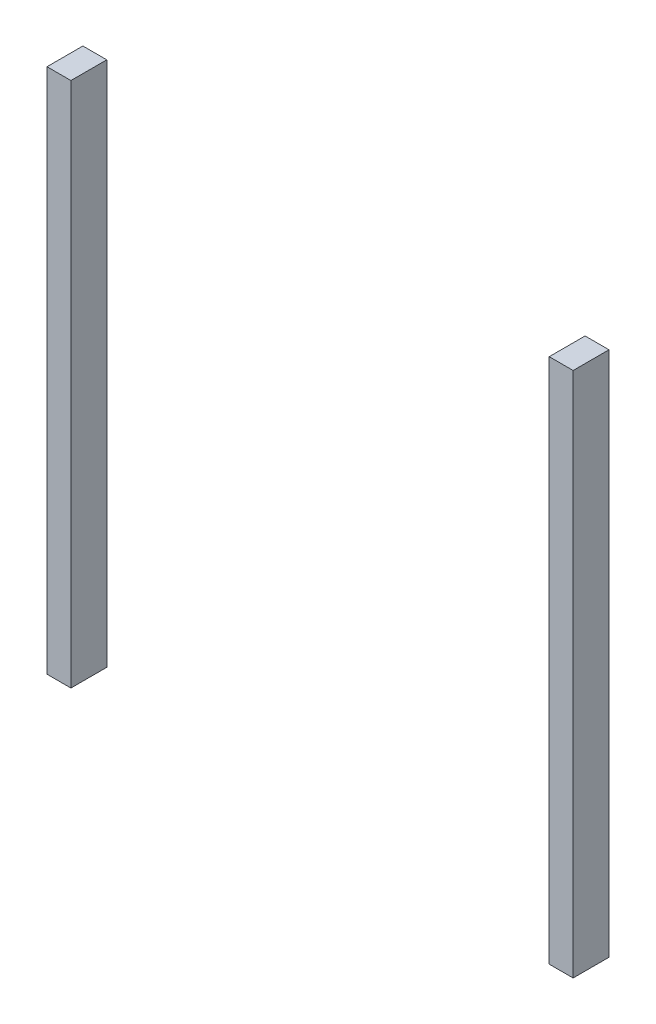
SolidWorks part; units mm, degrees
ref_plane "Front Plane" through (0, 0, 0) normal (0, 0, 1) x (1, 0, 0)
ref_plane "Top Plane" through (0, 0, 0) normal (0, 1, 0) x (1, 0, 0)
ref_plane "Right Plane" through (0, 0, 0) normal (1, 0, 0) x (0, 0, -1)
sketch "Sketch1" plane through (0, 0, 0) normal (0, 0, 1) x (1, 0, 0)
  line L0 (0, 139.7) -> (6.35, 139.7)
  line L1 (0, 0) -> (6.35, 0)
  line L2 (0, 0) -> (0, 139.7)
  line L3 (133.35, 139.7) -> (139.7, 139.7)
  line L4 (139.7, 0) -> (139.7, 139.7)
  line L5 (6.35, 139.7) -> (6.35, 0)
  line L6 (133.35, 139.7) -> (133.35, 0)
  line L7 (133.35, 0) -> (139.7, 0)
extrude "Boss-Extrude1" add sketch "Sketch1" along normal blind 9.525
